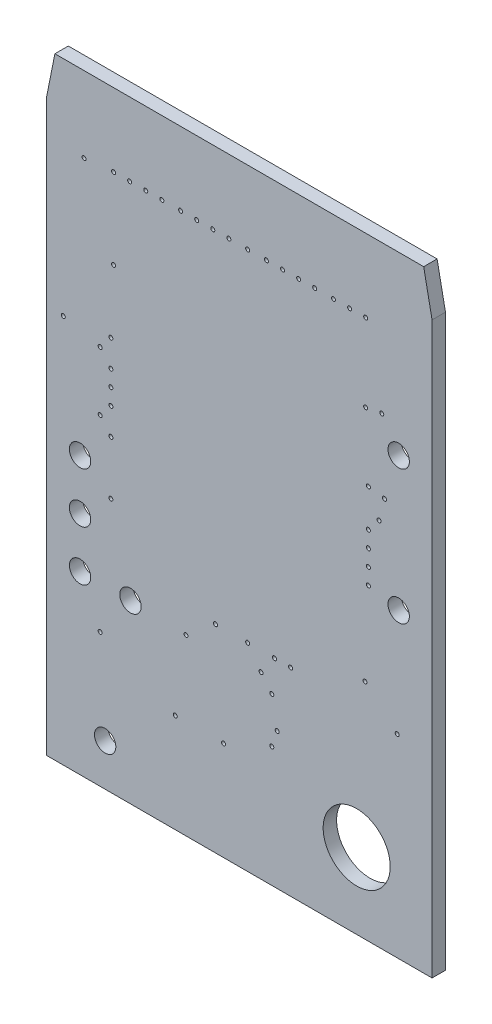
SolidWorks part; units mm, degrees
ref_plane "Front Plane" through (0, 0, 0) normal (0, 0, 1) x (1, 0, 0)
ref_plane "Top Plane" through (0, 0, 0) normal (0, 1, 0) x (1, 0, 0)
ref_plane "Right Plane" through (0, 0, 0) normal (1, 0, 0) x (0, 0, -1)
ref_plane "Dielectric_Layer Layer 1" through (0, 0, 0.508) normal (0, 0, 1) x (1, 0, 0)
sketch "Sketch1" plane through (0, 0, 0) normal (0, 0, 1) x (1, 0, 0)
  line L0 (0, 0) -> (0, 21.59)
  line L1 (0, 21.59) -> (0.3175, 23.1775)
  line L2 (0.3175, 23.1775) -> (14.2875, 23.1775)
  line L3 (14.2875, 23.1775) -> (14.605, 21.59)
  line L4 (14.605, 21.59) -> (14.605, 0)
  line L5 (14.605, 0) -> (0, 0)
extrude "Board_Outline" add sketch "Sketch1" along normal blind 0.508 separate body
sketch "Sketch2" plane through (0, 0, 0) normal (0, 0, 1) x (1, 0, 0)
  circle A0 centre (1.4224, 20.3073) radius 0.0762
  circle A1 centre (8.5344, 4.5593) radius 0.0762
  circle A2 centre (12.7, 17.5641) radius 0.0762
  circle A3 centre (12.065, 8.4582) radius 0.0762
  circle A4 centre (13.2842, 7.3406) radius 0.0762
  circle A5 centre (0.635, 14.732) radius 0.0762
  circle A6 centre (3.1496, 20.4089) radius 0.0762
  circle A7 centre (2.4384, 14.9225) radius 0.0762
  circle A8 centre (2.54, 20.4089) radius 0.0762
  circle A9 centre (2.54, 17.3609) radius 0.0762
  circle A10 centre (3.7592, 20.4089) radius 0.0762
  circle A11 centre (2.032, 14.4145) radius 0.0762
  circle A12 centre (4.3688, 20.4089) radius 0.0762
  circle A13 centre (2.4384, 13.9065) radius 0.0762
  circle A14 centre (5.08, 20.4089) radius 0.0762
  circle A15 centre (2.4384, 13.2969) radius 0.0762
  circle A16 centre (5.6896, 20.4089) radius 0.0762
  circle A17 centre (2.4384, 12.6873) radius 0.0762
  circle A18 centre (6.2992, 20.4089) radius 0.0762
  circle A19 centre (2.032, 12.1793) radius 0.0762
  circle A20 centre (6.9088, 20.4089) radius 0.0762
  circle A21 centre (2.4384, 11.6713) radius 0.0762
  circle A22 centre (7.62, 20.4089) radius 0.0762
  circle A23 centre (12.192, 11.6713) radius 0.0762
  circle A24 centre (12.0904, 20.4089) radius 0.0762
  circle A25 centre (12.0904, 17.4625) radius 0.0762
  circle A26 centre (11.4808, 20.4089) radius 0.0762
  circle A27 centre (12.192, 14.9225) radius 0.0762
  circle A28 centre (10.8712, 20.4089) radius 0.0762
  circle A29 centre (12.8016, 14.8209) radius 0.0762
  circle A30 centre (10.16, 20.4089) radius 0.0762
  circle A31 centre (12.5984, 14.0081) radius 0.0762
  circle A32 centre (9.5504, 20.4089) radius 0.0762
  circle A33 centre (12.192, 13.5001) radius 0.0762
  circle A34 centre (8.9408, 20.4089) radius 0.0762
  circle A35 centre (12.192, 12.8905) radius 0.0762
  circle A36 centre (8.3312, 20.4089) radius 0.0762
  circle A37 centre (12.192, 12.2809) radius 0.0762
  circle A38 centre (6.4008, 7.5057) radius 0.0762
  circle A39 centre (4.8768, 3.7465) radius 0.0762
  circle A40 centre (2.032, 5.0673) radius 0.0762
  circle A41 centre (5.2832, 6.5913) radius 0.0762
  circle A42 centre (7.62, 7.5057) radius 0.0762
  circle A43 centre (8.5344, 6.2865) radius 0.0762
  circle A44 centre (6.7056, 3.7465) radius 0.0762
  circle A45 centre (8.636, 7.5057) radius 0.0762
  circle A46 centre (9.2456, 7.5057) radius 0.0762
  circle A47 centre (8.128, 6.7945) radius 0.0762
  circle A48 centre (2.4384, 9.6393) radius 0.0762
  circle A49 centre (8.7376, 5.1689) radius 0.0762
extrude "NPTH" cut sketch "Sketch2" along normal through all
sketch "Sketch3" plane through (0, 0, 0) normal (0, 0, 1) x (1, 0, 0)
  circle A0 centre (1.27, 8.57) radius 0.405
  circle A1 centre (2.22, 1.59) radius 0.405
  circle A2 centre (1.27, 10.48) radius 0.405
  circle A3 centre (11.75, 2.86) radius 1.27
  circle A4 centre (1.27, 6.67) radius 0.405
  circle A5 centre (3.18, 6.67) radius 0.405
  circle A6 centre (13.34, 16.51) radius 0.405
  circle A7 centre (13.34, 11.43) radius 0.405
extrude "PTH" cut sketch "Sketch3" along normal through all
